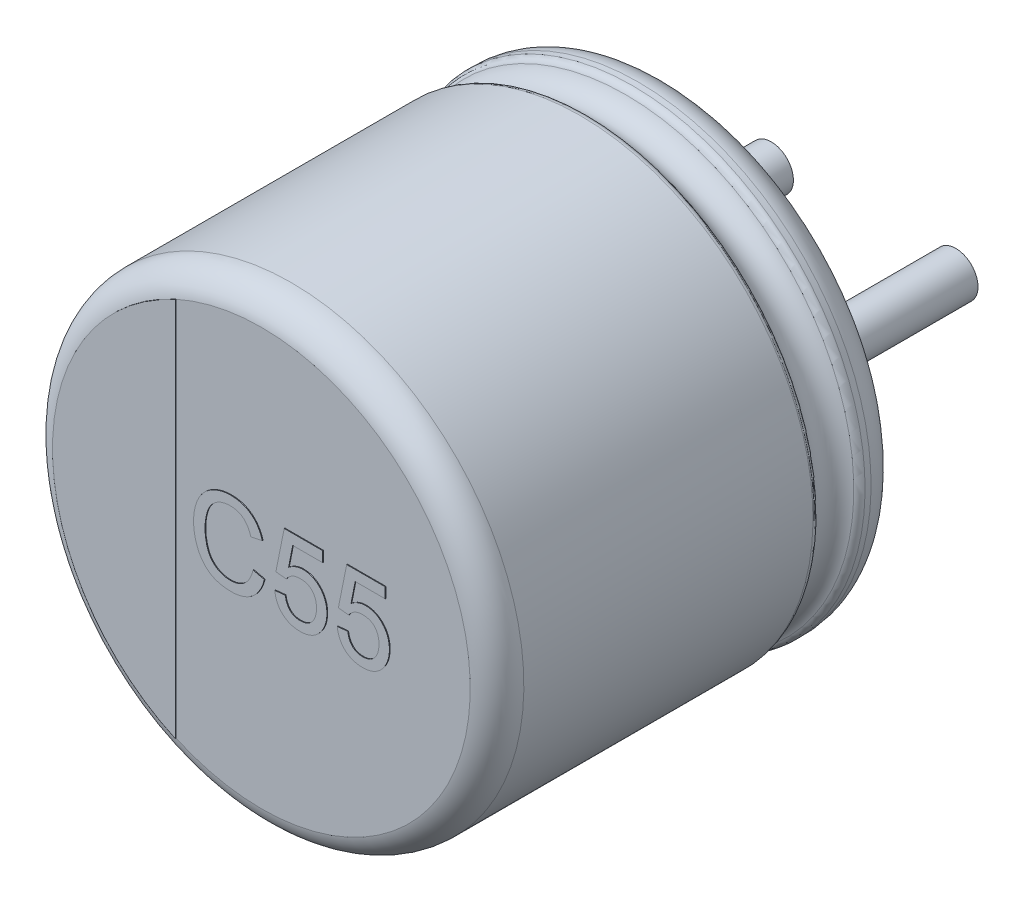
SolidWorks part; units mm, degrees
ref_plane "Plan de face" through (0, 0, 0) normal (0, 0, 1) x (1, 0, 0)
ref_plane "Plan de dessus" through (0, 0, 0) normal (0, 1, 0) x (1, 0, 0)
ref_plane "Plan de droite" through (0, 0, 0) normal (1, 0, 0) x (0, 0, -1)
sketch "Sketch10" plane through (0, 0, 0) normal (1, 0, 0) x (0, 0, -1)
  line L0 (18.1631, 0) -> (-18.9631, 0) construction
  line L1 (-5.5, 0) -> (-0.05, 0)
  line L2 (-5.5, 0) -> (-5.5, 2.8236)
  line L3 (-5.1, 3.15) -> (-1.1846, 3.15)
  line L4 (-0.05, 2.5531) -> (-0.05, 0)
  line L7 (-0.4794, 3.15) -> (-0.3982, 3.15)
  arc A0 (-5.5, 2.8236) -> (-5.1, 3.15) centre (-5.1068, 2.7501) cw
  arc A1 (-0.3982, 3.15) -> (-0.05, 2.5531) centre (-0.3982, 2.75) cw
  arc A2 (-0.5713, 3.0894) -> (-1.0926, 3.0894) centre (-0.832, 3.201) cw
  arc A3 (-1.0926, 3.0894) -> (-1.1846, 3.15) centre (-1.1846, 3.05) ccw
  arc A4 (-0.5713, 3.0894) -> (-0.4794, 3.15) centre (-0.4794, 3.05) cw
  point P4 (0.57, 0)
  point P13 (-5.5, 3.15)
  dimension "D2" = 0.4
  dimension "D3" = 0.4
  dimension "D4" = 0.1
  dimension "D5" = 0.1
  dimension "D1" = 3.15
  dimension "D7" = 0.05
  dimension "D8" = 3.15
revolve "Повернуть1" add sketch "Sketch10" angle 360 about L0
sketch "Эскиз2" plane through (0, 0, 0.05) normal (0, 0, -1) x (-1, 0, 0)
  line L1 (0, 0.7993) -> (0, -1.0496) construction
  line L2 (-1.25, 0) -> (3.6313, 0) construction
  circle A3 centre (-1.25, 0) radius 0.3
  circle A7 centre (1.25, 0) radius 0.3
  dimension "D1" = 2.5
extrude "Бобышка-Вытянуть1" add sketch "Эскиз2" along normal blind 2.7
sketch "Эскиз4" plane through (0, 0, 5.5) normal (0, 0, 1) x (1, 0, 0)
  line L0 (-1.1603, -2.5741) -> (-1.1603, 2.5741)
  circle A1 centre (0, 0) radius 2.8236 construction
  arc A2 (-1.1603, 2.5741) -> (-1.1603, -2.5741) centre (0, 0) ccw
extrude "Бобышка-Вытянуть2" add sketch "Эскиз4" along normal blind 0.01
sketch "Эскиз5" plane through (0, 0, 5.5) normal (0, 0, 1) x (1, 0, 0)
  text T0 "C55" font "Arial" height 1.1
extrude "Текст" add sketch "Эскиз5" along normal blind 0.01
sketch "Эскиз6" plane through (0, 0, 0.05) normal (0, 0, -1) x (-1, 0, 0)
  line L0 (-1.25, 0.4) -> (-1.6248, 0.4)
  line L1 (-1.25, -0.4) -> (-1.6248, -0.4)
  line L2 (1.25, -0.4) -> (1.6248, -0.4)
  line L3 (1.25, 0.4) -> (1.6248, 0.4)
  arc A0 (-1.8569, -0.7429) -> (1.8569, -0.7429) centre (0, 0) ccw
  arc A1 (-1.25, -0.4) -> (-1.25, 0.4) centre (-1.25, 0) ccw
  arc A2 (1.25, 0.4) -> (1.25, -0.4) centre (1.25, 0) ccw
  arc A3 (1.8569, 0.7429) -> (-1.8569, 0.7429) centre (0, 0) ccw
  arc A4 (1.6248, 0.4) -> (1.8569, 0.7429) centre (1.6248, 0.65) ccw
  arc A5 (1.6248, -0.4) -> (1.8569, -0.7429) centre (1.6248, -0.65) cw
  arc A6 (-1.8569, -0.7429) -> (-1.6248, -0.4) centre (-1.6248, -0.65) cw
  arc A7 (-1.6248, 0.4) -> (-1.8569, 0.7429) centre (-1.6248, 0.65) cw
  point P7 (1.9596, 0.4)
  point P23 (0, -2)
  point P24 (0, 2)
  dimension "D1" = 0.25
  dimension "D2" = 4
extrude "Бобышка-Вытянуть5" add sketch "Эскиз6" along normal blind 0.05 contours A3 A7 L0 A1 L1 A6 A0 A5 L2 A2 L3 A4
